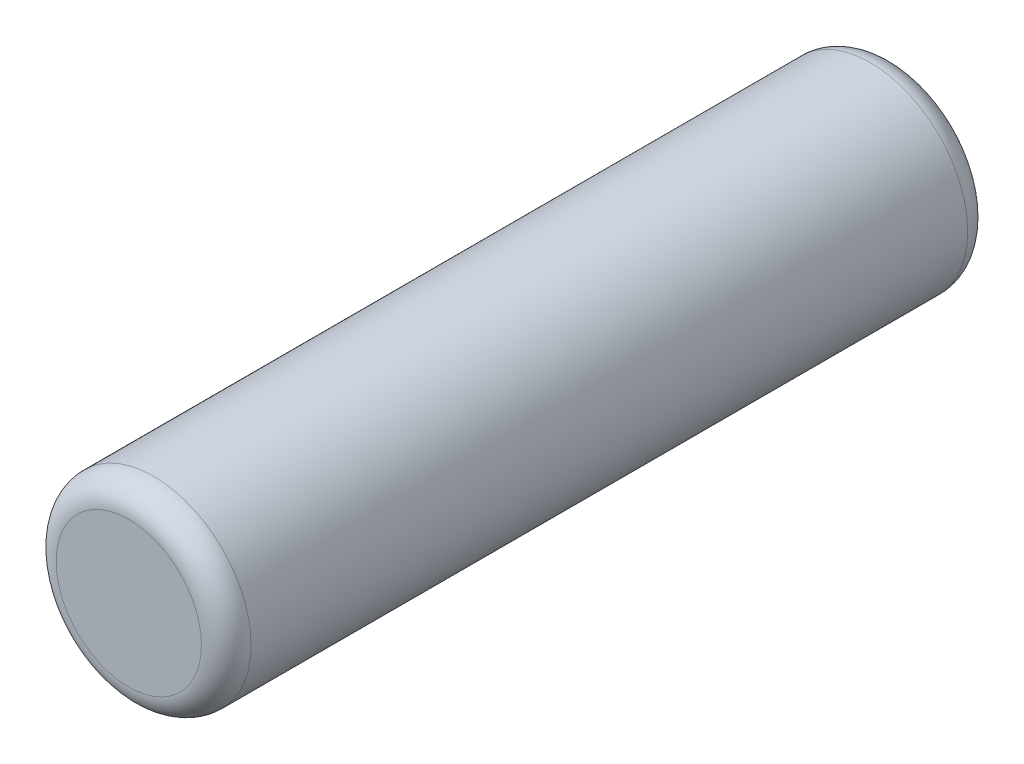
SolidWorks part; units mm, degrees
material "AISI 1015 Steel, Cold Drawn (SS)"
ref_plane "Plane1" through (0, 0, 0) normal (0, 0, 1) x (1, 0, 0)
ref_plane "Plane2" through (0, 0, 0) normal (0, 1, 0) x (-1, 0, 0)
ref_plane "Plane3" through (0, 0, 0) normal (1, 0, 0) x (0, 0, -1)
sketch "Sketch1" plane through (0, 0, 0) normal (0, 0, 1) x (1, 0, 0)
  circle A0 centre (0, 0) radius 1.9939
  dimension "D1" = 3.9878
extrude "Base-Extrude" add sketch "Sketch1" along normal mid plane 15.6718
fillet "Fillet1" radius 0.508 2 edges at (1.9939, 0, 7.8359) (1.9939, 0, -7.8359)
